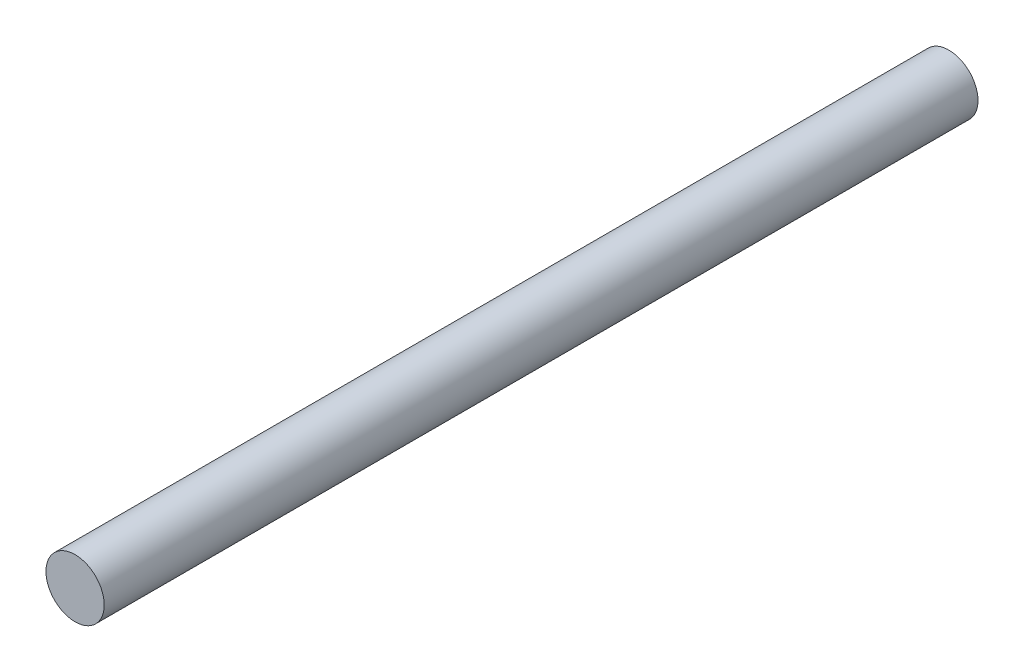
SolidWorks part; units mm, degrees
ref_plane "Alzado" through (0, 0, 0) normal (0, 0, 1) x (1, 0, 0)
ref_plane "Planta" through (0, 0, 0) normal (0, 1, 0) x (1, 0, 0)
ref_plane "Vista lateral" through (0, 0, 0) normal (1, 0, 0) x (0, 0, -1)
sketch "Croquis1" plane through (0, 0, 0) normal (0, 0, 1) x (1, 0, 0)
  circle A0 centre (0, 0) radius 10
  dimension "D1" = 20
extrude "Saliente-Extruir1" add sketch "Croquis1" along normal blind 300
